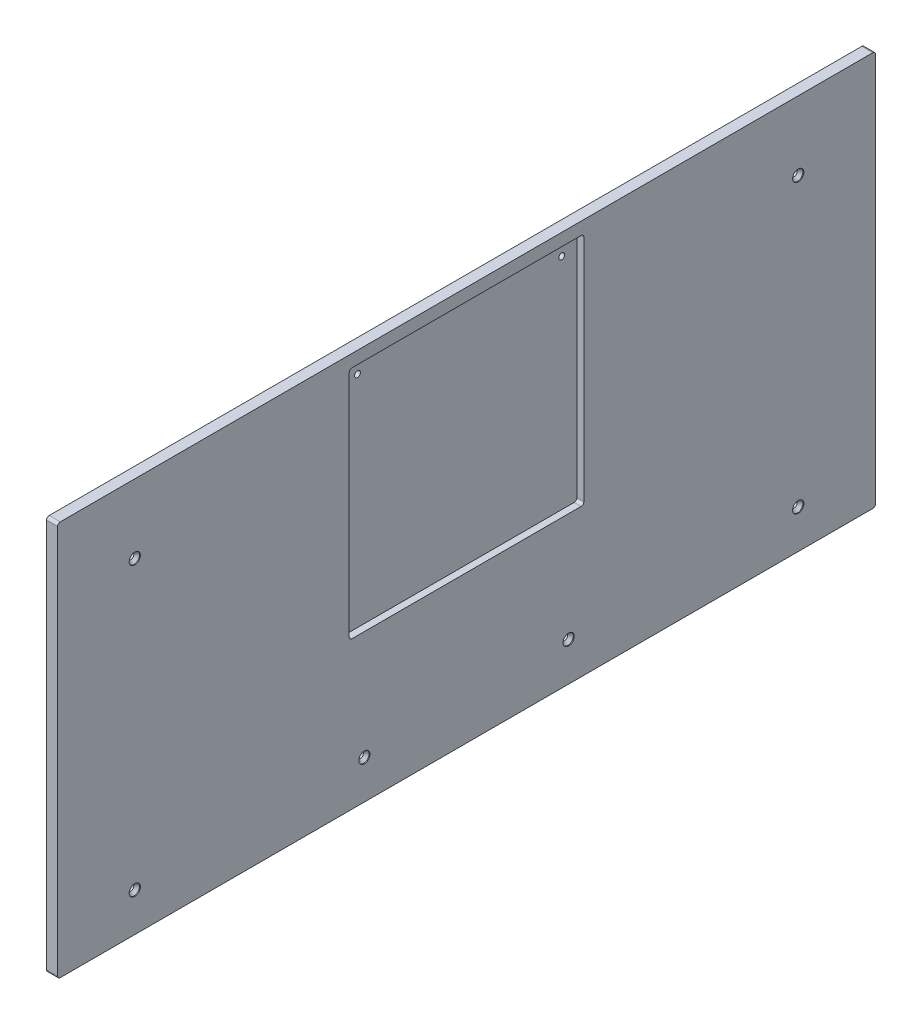
SolidWorks part; units mm, degrees
material "PE High Density"
ref_plane "Front Plane" through (0, 0, 0) normal (0, 0, 1) x (1, 0, 0)
ref_plane "Top Plane" through (0, 0, 0) normal (0, 1, 0) x (1, 0, 0)
ref_plane "Right Plane" through (0, 0, 0) normal (1, 0, 0) x (0, 0, -1)
sketch "Sketch1" plane through (0, 0, 0) normal (1, 0, 0) x (0, 0, -1)
  line L1 (0, 0) -> (940.882, 0)
  line L2 (0, 0) -> (0, 454.025)
  line L3 (0, 454.025) -> (940.882, 454.025)
  line L4 (940.882, 0) -> (940.882, 454.025)
  circle A8 centre (352.966, 422.275) radius 3.3734
  circle A9 centre (587.916, 422.275) radius 3.3734
  dimension "D4" = 6.7469
  dimension "D5" = 352.966
  dimension "D1" = 454.025
  dimension "D2" = 940.882
  dimension "D3" = 352.966
  dimension "D10" = 31.75
extrude "Boss-Extrude1" add sketch "Sketch1" along normal blind 12.7
fillet "Fillet1" radius 3.175 4 edges at (6.35, 454.025, -940.882) (6.35, 0, -940.882) (6.35, 0, 0) (6.35, 454.025, 0)
sketch "Sketch2" plane through (12.7, 0, 0) normal (1, 0, 0) x (0, 0, -1)
  line L0 (937.707, 454.025) -> (3.175, 454.025) construction
  line L1 (335.5035, 439.7375) -> (605.3785, 439.7375)
  line L2 (335.5035, 439.7375) -> (335.5035, 169.8625)
  line L3 (335.5035, 169.8625) -> (605.3785, 169.8625)
  line L4 (605.3785, 439.7375) -> (605.3785, 169.8625)
  circle A0 centre (352.966, 422.275) radius 3.3734 construction
  point P6 (470.441, 454.025)
  point P7 (470.441, 439.7375)
  dimension "D1" = 269.875
  dimension "D2" = 269.875
  dimension "D3" = 17.4625
extrude "Cut-Extrude1" cut sketch "Sketch2" against normal blind 7.9375
fillet "Fillet2" radius 3.175 4 edges at (8.7312, 439.7375, -335.5035) (8.7312, 439.7375, -605.3785) (8.7312, 169.8625, -335.5035) (8.7312, 169.8625, -605.3785)
hole_wizard "CSK for 1/4 Flat Head Machine Screw1" positions "Sketch4" profile "Sketch5" countersink size "1/4" standard "ANSI Inch" end condition through all
sketch "Sketch4" plane through (12.7, 0, 0) normal (1, 0, 0) x (0, 0, -1)
  line L0 (0, 450.85) -> (0, 3.175) construction
  line L2 (3.175, 0) -> (937.707, 0) construction
  line L3 (940.882, 3.175) -> (940.882, 450.85) construction
  point P0 (88.9, 374.65)
  point P2 (851.982, 374.65)
  point P4 (88.9, 44.45)
  point P6 (352.966, 44.45)
  point P8 (587.916, 44.45)
  point P10 (851.982, 44.45)
  dimension "D1" = 88.9
  dimension "D2" = 330.2
  dimension "D3" = 44.45
  dimension "D4" = 264.066
  dimension "D5" = 264.066
  dimension "D6" = 88.9
sketch "Sketch5" plane through (12.7, 374.65, -88.9) normal (0, 1, 0) x (0, 0, -1)
  line L0 (0, 0) -> (0, 12.7)
  line L1 (0, 12.7) -> (3.3782, 12.7)
  line L2 (3.3782, 12.7) -> (3.3782, 4.5369)
  line L3 (3.3782, 4.5369) -> (6.4389, 1.016)
  line L4 (6.4389, 1.016) -> (6.4389, 0)
  line L6 (6.4389, 0) -> (0, 0)
  line L7 (-3.3782, 4.5369) -> (-6.4389, 1.016) construction
  line L11 (0, -6.35) -> (0, 107.95) construction
  dimension "Thru Hole Dia." = 6.7564
  dimension "Thru Hole Depth" = 12.7
  dimension "C'Sink Dia." = 12.8778
  dimension "C'Sink Angle" = 82
  dimension "Head Clearance" = 1.016
